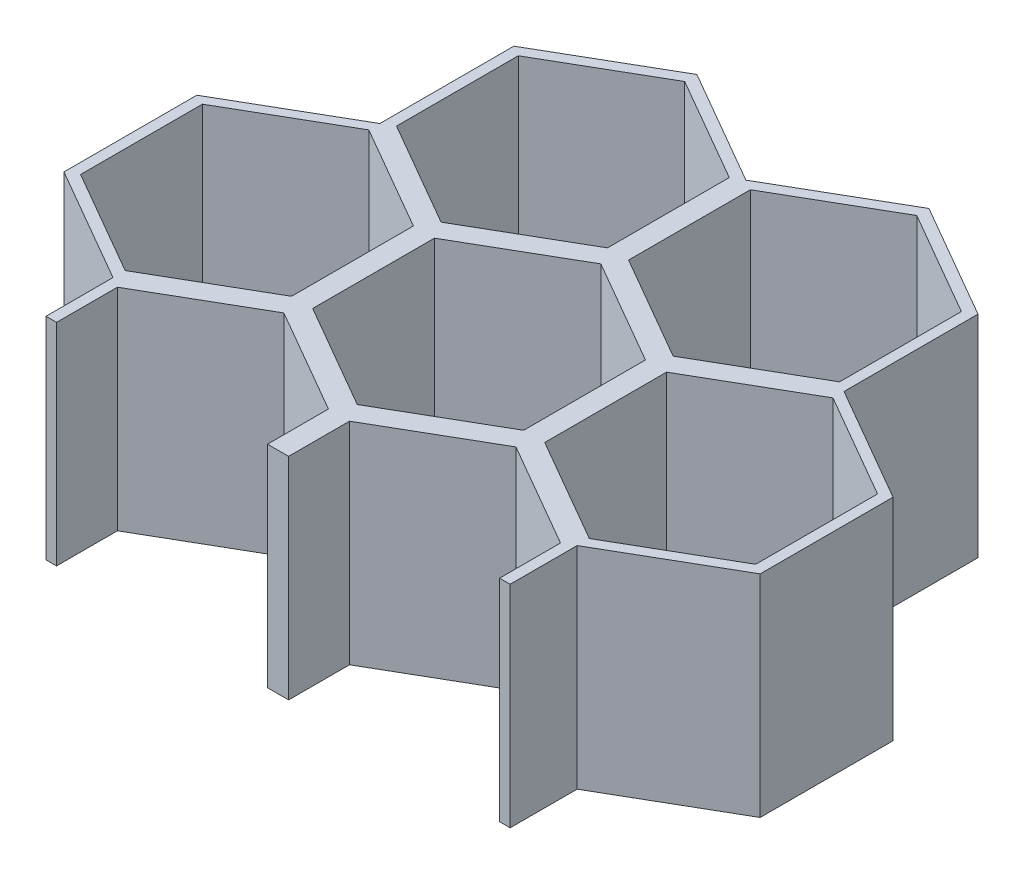
SolidWorks part; units mm, degrees
ref_plane "Front Plane" through (0, 0, 0) normal (0, 0, 1) x (1, 0, 0)
ref_plane "Top Plane" through (0, 0, 0) normal (0, 1, 0) x (1, 0, 0)
ref_plane "Right Plane" through (0, 0, 0) normal (1, 0, 0) x (0, 0, -1)
sketch "Sketch1" plane through (0, 0, 0) normal (0, 1, 0) x (1, 0, 0)
  line L0 (22, 11.547) -> (12, 5.7735)
  line L1 (0, 11.547) -> (-10, 5.7735)
  line L2 (-10, 5.7735) -> (-10, -5.7735)
  line L3 (-10, -5.7735) -> (0, -11.547)
  line L4 (0, -11.547) -> (10, -5.7735)
  line L5 (10, -5.7735) -> (10, 5.7735)
  line L6 (10, 5.7735) -> (0, 11.547)
  line L7 (11, -30.5996) -> (21, -24.8261)
  line L8 (21, -24.8261) -> (21, -13.2791)
  line L9 (21, -13.2791) -> (11, -7.5056)
  line L10 (11, -7.5056) -> (1, -13.2791)
  line L11 (1, -13.2791) -> (1, -24.8261)
  line L12 (1, -24.8261) -> (11, -30.5996)
  line L13 (12, 5.7735) -> (12, -5.7735)
  line L14 (12, -5.7735) -> (22, -11.547)
  line L15 (22, -11.547) -> (32, -5.7735)
  line L16 (32, -5.7735) -> (32, 5.7735)
  line L17 (32, 5.7735) -> (22, 11.547)
  line L18 (33, -30.5996) -> (43, -24.8261)
  line L19 (43, -24.8261) -> (43, -13.2791)
  line L20 (43, -13.2791) -> (33, -7.5056)
  line L21 (33, -7.5056) -> (23, -13.2791)
  line L22 (23, -13.2791) -> (23, -24.8261)
  line L23 (23, -24.8261) -> (33, -30.5996)
  line L24 (44, 11.547) -> (34, 5.7735)
  line L25 (34, 5.7735) -> (34, -5.7735)
  line L26 (34, -5.7735) -> (44, -11.547)
  line L27 (44, -11.547) -> (54, -5.7735)
  line L28 (54, -5.7735) -> (54, 5.7735)
  line L29 (54, 5.7735) -> (44, 11.547)
  line L30 (55, -30.5996) -> (65, -24.8261)
  line L31 (65, -24.8261) -> (65, -13.2791)
  line L32 (65, -13.2791) -> (55, -7.5056)
  line L33 (55, -7.5056) -> (45, -13.2791)
  line L34 (45, -13.2791) -> (45, -24.8261)
  line L35 (45, -24.8261) -> (55, -30.5996)
  line L36 (22, 49.547) -> (12, 43.7735)
  line L37 (12, 43.7735) -> (12, 32.2265)
  line L38 (12, 32.2265) -> (22, 26.453)
  line L39 (22, 26.453) -> (32, 32.2265)
  line L40 (32, 32.2265) -> (32, 43.7735)
  line L41 (32, 43.7735) -> (22, 49.547)
  line L42 (33, 7.4004) -> (43, 13.1739)
  line L43 (43, 13.1739) -> (43, 24.7209)
  line L44 (43, 24.7209) -> (33, 30.4944)
  line L45 (33, 30.4944) -> (23, 24.7209)
  line L46 (23, 24.7209) -> (23, 13.1739)
  line L47 (23, 13.1739) -> (33, 7.4004)
  line L48 (44, 49.547) -> (34, 43.7735)
  line L49 (34, 43.7735) -> (34, 32.2265)
  line L50 (34, 32.2265) -> (44, 26.453)
  line L51 (44, 26.453) -> (54, 32.2265)
  line L52 (54, 32.2265) -> (54, 43.7735)
  line L53 (54, 43.7735) -> (44, 49.547)
  line L54 (55, 7.4004) -> (65, 13.1739)
  line L55 (65, 13.1739) -> (65, 24.7209)
  line L56 (65, 24.7209) -> (55, 30.4944)
  line L57 (55, 30.4944) -> (45, 24.7209)
  line L58 (45, 24.7209) -> (45, 13.1739)
  line L59 (45, 13.1739) -> (55, 7.4004)
  line L60 (0, 49.547) -> (-10, 43.7735)
  line L61 (-10, 43.7735) -> (-10, 32.2265)
  line L62 (-10, 32.2265) -> (0, 26.453)
  line L63 (0, 26.453) -> (10, 32.2265)
  line L64 (10, 32.2265) -> (10, 43.7735)
  line L65 (10, 43.7735) -> (0, 49.547)
  line L66 (11, 7.4004) -> (21, 13.1739)
  line L67 (21, 13.1739) -> (21, 24.7209)
  line L68 (21, 24.7209) -> (11, 30.4944)
  line L69 (11, 30.4944) -> (1, 24.7209)
  line L70 (1, 24.7209) -> (1, 13.1739)
  line L71 (1, 13.1739) -> (11, 7.4004)
  line L72 (66, 11.547) -> (56, 5.7735)
  line L74 (11, -19.0526) -> (11, 38)
  line L75 (11, 38) -> (66, 38)
  line L77 (56, 5.7735) -> (56, -5.7735)
  line L78 (56, -5.7735) -> (66, -11.547)
  line L79 (66, -11.547) -> (76, -5.7735)
  line L80 (76, -5.7735) -> (76, 5.7735)
  line L81 (76, 5.7735) -> (66, 11.547)
  line L82 (77, -30.5996) -> (87, -24.8261)
  line L83 (87, -24.8261) -> (87, -13.2791)
  line L84 (87, -13.2791) -> (77, -7.5056)
  line L85 (77, -7.5056) -> (67, -13.2791)
  line L86 (67, -13.2791) -> (67, -24.8261)
  line L87 (67, -24.8261) -> (77, -30.5996)
  line L88 (66, 49.547) -> (56, 43.7735)
  line L89 (56, 43.7735) -> (56, 32.2265)
  line L90 (56, 32.2265) -> (66, 26.453)
  line L91 (66, 26.453) -> (76, 32.2265)
  line L92 (76, 32.2265) -> (76, 43.7735)
  line L93 (76, 43.7735) -> (66, 49.547)
  line L94 (77, 7.4004) -> (87, 13.1739)
  line L95 (87, 13.1739) -> (87, 24.7209)
  line L96 (87, 24.7209) -> (77, 30.4944)
  line L97 (77, 30.4944) -> (67, 24.7209)
  line L98 (67, 24.7209) -> (67, 13.1739)
  line L99 (67, 13.1739) -> (77, 7.4004)
  line L100 (11, -19.0526) -> (77, -19.0526)
  line L101 (77, -19.0526) -> (77, 38)
  line L102 (77, 38) -> (66, 38)
  circle A0 centre (0, 0) radius 10 construction
  circle A1 centre (11, -19.0526) radius 10 construction
  circle A2 centre (22, 0) radius 10 construction
  circle A3 centre (33, -19.0526) radius 10 construction
  circle A4 centre (44, 0) radius 10 construction
  circle A5 centre (55, -19.0526) radius 10 construction
  circle A6 centre (22, 38) radius 10 construction
  circle A7 centre (33, 18.9474) radius 10 construction
  circle A8 centre (44, 38) radius 10 construction
  circle A9 centre (55, 18.9474) radius 10 construction
  circle A10 centre (0, 38) radius 10 construction
  circle A11 centre (11, 18.9474) radius 10 construction
  circle A12 centre (66, 0) radius 10 construction
  circle A13 centre (77, -19.0526) radius 10 construction
  circle A14 centre (66, 38) radius 10 construction
  circle A15 centre (77, 18.9474) radius 10 construction
  dimension "D1" = 20
  dimension "D2" = 2
  dimension "D3" = 1
  dimension "D4" = 4
  dimension "D5" = 2
extrude "Boss-Extrude2" add sketch "Sketch1" along normal blind 20
sketch "Sketch2" plane through (0, 20, 0) normal (0, 1, 0) x (1, 0, 0)
  line L0 (11, 6.2457) -> (22, 12.5966)
  line L1 (11, -7.5056) -> (11, 7.4004) construction
  line L2 (22, 12.5966) -> (22, 25.2983)
  line L3 (22, 25.2983) -> (11, 31.6491)
  line L4 (11, 30.4944) -> (11, 38) construction
  line L5 (11, -6.3509) -> (22, -12.7017)
  line L6 (22, -12.7017) -> (22, -19.0526)
  line L9 (21, -13.2791) -> (11, -7.5056) construction
  line L11 (11, 7.4004) -> (21, 13.1739) construction
  line L13 (21, 24.7209) -> (11, 30.4944) construction
  line L14 (11, 6.2457) -> (11, -6.3509)
  line L15 (11, 31.6491) -> (2.2959, -19.0526)
  line L16 (2.2959, -19.0526) -> (22, -19.0526)
  line L17 (21, -19.0526) -> (23, -19.0526) construction
  line L19 (44, 26.453) -> (44, -11.547) construction
  line L20 (77, 31.6491) -> (85.7041, -19.0526)
  line L21 (66, 25.2983) -> (77, 31.6491)
  line L22 (66, 12.5966) -> (66, 25.2983)
  line L23 (77, 6.2457) -> (66, 12.5966)
  line L24 (77, 6.2457) -> (77, -6.3509)
  line L25 (77, -6.3509) -> (66, -12.7017)
  line L26 (66, -12.7017) -> (66, -19.0526)
  line L27 (85.7041, -19.0526) -> (66, -19.0526)
  point P18 (22, -19.0526)
  dimension "D1" = 1
  dimension "D2" = 1
  dimension "D3" = 1
extrude "Cut-Extrude1" cut sketch "Sketch2" against normal through all
sketch "Sketch4" plane through (0, 20, 0) normal (0, 1, 0) x (1, 0, 0)
  line L0 (22, 25.2983) -> (33, 31.6491)
  line L1 (33, 31.6491) -> (44, 25.2983)
  line L2 (44, 25.2983) -> (55, 31.6491)
  line L3 (55, 31.6491) -> (66, 25.2983)
  line L4 (56, 32.2265) -> (66, 26.453) construction
  line L5 (43, 24.7209) -> (33, 30.4944) construction
  line L6 (33, 30.4944) -> (23, 24.7209) construction
  line L7 (22, 25.2983) -> (11, 31.6491)
  line L8 (11, 31.6491) -> (11, 38)
  line L9 (11, 38) -> (77, 38)
  line L10 (77, 38) -> (77, 31.6491)
  line L11 (77, 31.6491) -> (66, 25.2983)
extrude "Cut-Extrude2" cut sketch "Sketch4" against normal through all
equation "\"parois_t\"= 2mm"
equation "\"panneau_t\"= 20mm"
equation "\"entreplat_interne\"= 20mm"
equation "\"D1@Sketch1\"=\"entreplat_interne\""
equation "\"D2@Sketch1\"=\"parois_t\""
